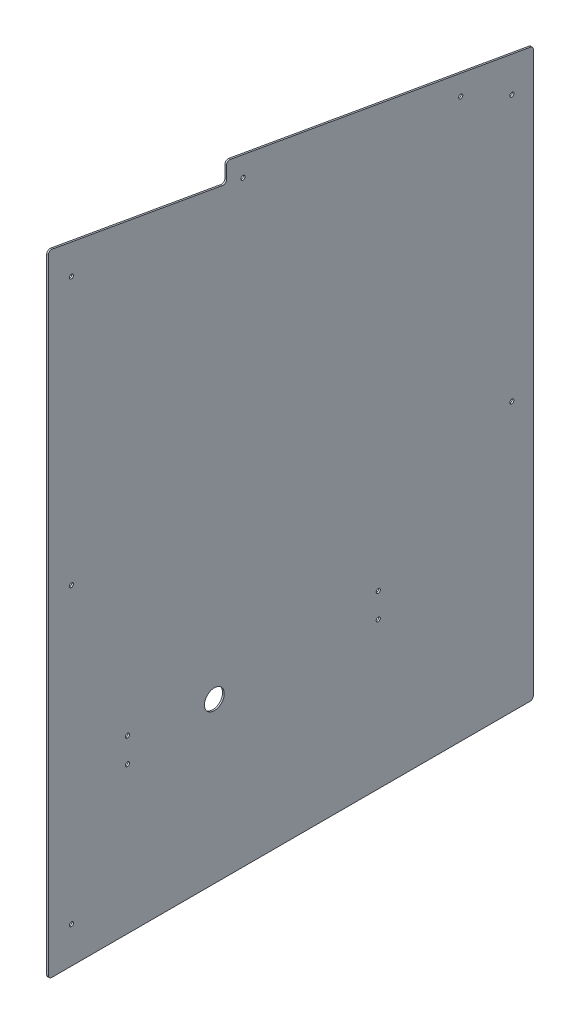
SolidWorks part; units mm, degrees
material "PC High Viscosity"
ref_plane "Front Plane" through (0, 0, 0) normal (0, 0, 1) x (1, 0, 0)
ref_plane "Top Plane" through (0, 0, 0) normal (0, 1, 0) x (1, 0, 0)
ref_plane "Right Plane" through (0, 0, 0) normal (1, 0, 0) x (0, 0, -1)
sketch "Sketch1" plane through (0, 0, 0) normal (1, 0, 0) x (0, 0, -1)
  line L0 (0, 0) -> (933.45, 0)
  line L1 (933.45, 0) -> (933.45, 1089.025)
  line L2 (933.45, 1089.025) -> (342.9, 1193.1549)
  line L3 (342.9, 1193.1549) -> (342.9, 1154.4671)
  line L4 (342.9, 1154.4671) -> (0, 1214.9297)
  line L5 (0, 1214.9297) -> (0, 0)
  dimension "D1" = 933.45
  dimension "D2" = 1089.025
  dimension "D3" = 38.1
  dimension "D4" = 342.9
  dimension "D5" = 100
extrude "Boss-Extrude1" add sketch "Sketch1" along normal blind 3.175
sketch "Sketch2" plane through (3.175, 0, 0) normal (1, 0, 0) x (0, 0, -1)
  line L0 (0, 1214.9297) -> (0, 0) construction
  line L1 (0, 0) -> (933.45, 0) construction
  circle A0 centre (319.532, 307.34) radius 19.05
  dimension "D1" = 38.1
  dimension "D2" = 319.532
  dimension "D3" = 307.34
extrude "Cut-Extrude1" cut sketch "Sketch2" against normal through all
fillet "Fillet1" radius 6.35 6 edges at (1.5875, 0, -933.45) (1.5875, 0, 0) (1.5875, 1089.025, -933.45) (1.5875, 1193.1549, -342.9) (1.5875, 1154.4671, -342.9) (1.5875, 1214.9297, 0)
hole_wizard "5/16 (0.3125) Diameter Hole1" positions "Sketch3" profile "Sketch4" hole size "5/16" standard "ANSI Inch" end condition through all
sketch "Sketch3" plane through (3.175, 0, 0) normal (1, 0, 0) x (0, 0, -1)
  line L0 (0, 1207.362) -> (0, 6.35) construction
  line L1 (928.2027, 1089.9502) -> (350.3527, 1191.8408) construction
  line L2 (6.35, 0) -> (927.1, 0) construction
  line L3 (933.45, 6.35) -> (933.45, 1083.6967) construction
  point P0 (44.45, 1149.35)
  point P2 (44.45, 635)
  point P4 (152.4, 330.2)
  point P6 (152.4, 282.575)
  point P8 (635, 330.2)
  point P10 (635, 282.575)
  point P12 (892.175, 517.525)
  point P14 (892.175, 1028.7)
  point P16 (374.65, 1148.8688)
  point P18 (793.75, 1074.9701)
  point P20 (44.45, 69.85)
  dimension "D1" = 44.45
  dimension "D2" = 38.1
  dimension "D3" = 38.1
  dimension "D4" = 282.575
  dimension "D5" = 330.2
  dimension "D6" = 41.275
  dimension "D7" = 69.85
  dimension "D8" = 635
  dimension "D9" = 1149.35
  dimension "D10" = 152.4
  dimension "D11" = 635
  dimension "D12" = 517.525
  dimension "D13" = 1028.7
  dimension "D14" = 139.7
  dimension "D15" = 558.8
sketch "Sketch4" plane through (3.175, 1149.35, -44.45) normal (0, 1, 0) x (0, 0, -1)
  line L0 (0, 0) -> (0, 3.175)
  line L1 (0, 3.175) -> (3.9688, 3.175)
  line L2 (3.9688, 3.175) -> (3.9687, 0)
  line L5 (3.9687, 0) -> (0, 0)
  line L11 (0, -6.35) -> (0, 107.95) construction
  dimension "Thru Hole Dia." = 7.9375
  dimension "Thru Hole Depth" = 3.175
